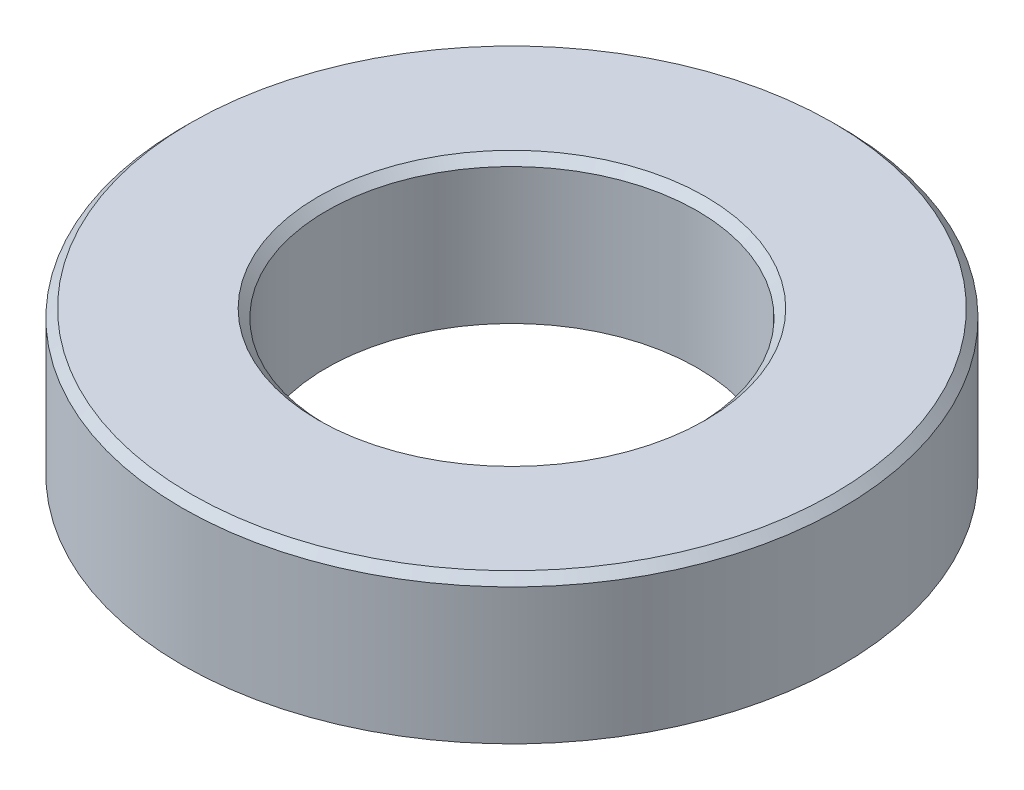
SolidWorks part; units mm, degrees
ref_plane "정면" through (0, 0, 0) normal (0, 0, 1) x (1, 0, 0)
ref_plane "윗면" through (0, 0, 0) normal (0, 1, 0) x (1, 0, 0)
ref_plane "우측면" through (0, 0, 0) normal (1, 0, 0) x (0, 0, -1)
sketch "스케치1" plane through (0, 0, 0) normal (0, 1, 0) x (1, 0, 0)
  circle A0 centre (0, 0) radius 4.5
  circle A1 centre (0, 0) radius 8
  dimension "D1" = 9
  dimension "D2" = 16
extrude "보스-돌출1" add sketch "스케치1" along normal blind 3.5
chamfer "모따기1" distance 0.2 angle 45 2 edges at (0, 3.5, 4.5) (0, 3.5, 8)
